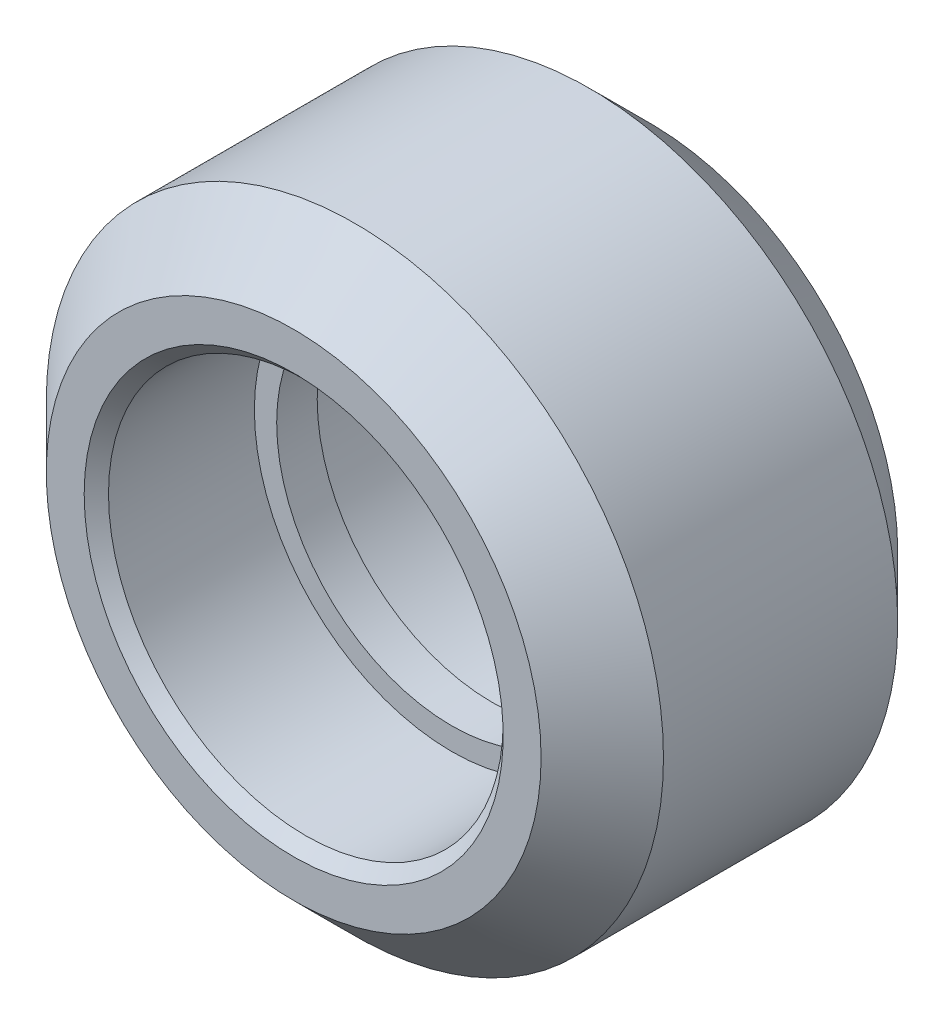
SolidWorks part; units mm, degrees
ref_plane "Front Plane" through (0, 0, 0) normal (0, 0, 1) x (1, 0, 0)
ref_plane "Top Plane" through (0, 0, 0) normal (0, 1, 0) x (1, 0, 0)
ref_plane "Right Plane" through (0, 0, 0) normal (1, 0, 0) x (0, 0, -1)
sketch "Sketch1" plane through (0, 0, 0) normal (1, 0, 0) x (0, 0, -1)
  line L0 (0, 0) -> (15, 0) construction
  line L1 (0, 0) -> (0, 7.615) construction
  line L2 (-2.89, 7.615) -> (2.89, 7.615) construction
  line L3 (-4.4, 6.105) -> (4.4, 6.105) construction
  line L4 (-4.4, 4.87) -> (4.4, 4.87) construction
  line L5 (-0.5, 4.32) -> (0.5, 4.32) construction
  line L6 (0.5, 4.32) -> (-0.5, 4.32)
  line L7 (-0.5, 4.32) -> (-0.5, 4.87)
  line L8 (-0.5, 4.87) -> (-4.4, 4.87)
  line L9 (-4.4, 4.87) -> (-4.4, 6.105)
  line L10 (-4.4, 6.105) -> (-2.89, 7.615)
  line L11 (-2.89, 7.615) -> (2.89, 7.615)
  line L12 (4.4, 6.105) -> (2.89, 7.615)
  line L13 (4.4, 4.87) -> (4.4, 6.105)
  line L14 (0.5, 4.87) -> (4.4, 4.87)
  line L15 (0.5, 4.32) -> (0.5, 4.87)
  point P12 (0, 4.32)
  point P13 (0, 4.87)
  point P14 (0, 6.105)
  point P15 (0, 7.615)
  point P19 (0, 4.32)
  dimension "D1" = 7.615
  dimension "D2" = 15
  dimension "D3" = 4.87
  dimension "D4" = 5.78
  dimension "D5" = 8.8
  dimension "D6" = 1
  dimension "D7" = 4.32
  dimension "D8" = 6.105
revolve "Revolve1" add sketch "Sketch1" angle 360 about L0
chamfer "Chamfer1" distance 0.3 angle 45 2 edges at (4.87, 0, -4.4) (4.87, 0, 4.4)
